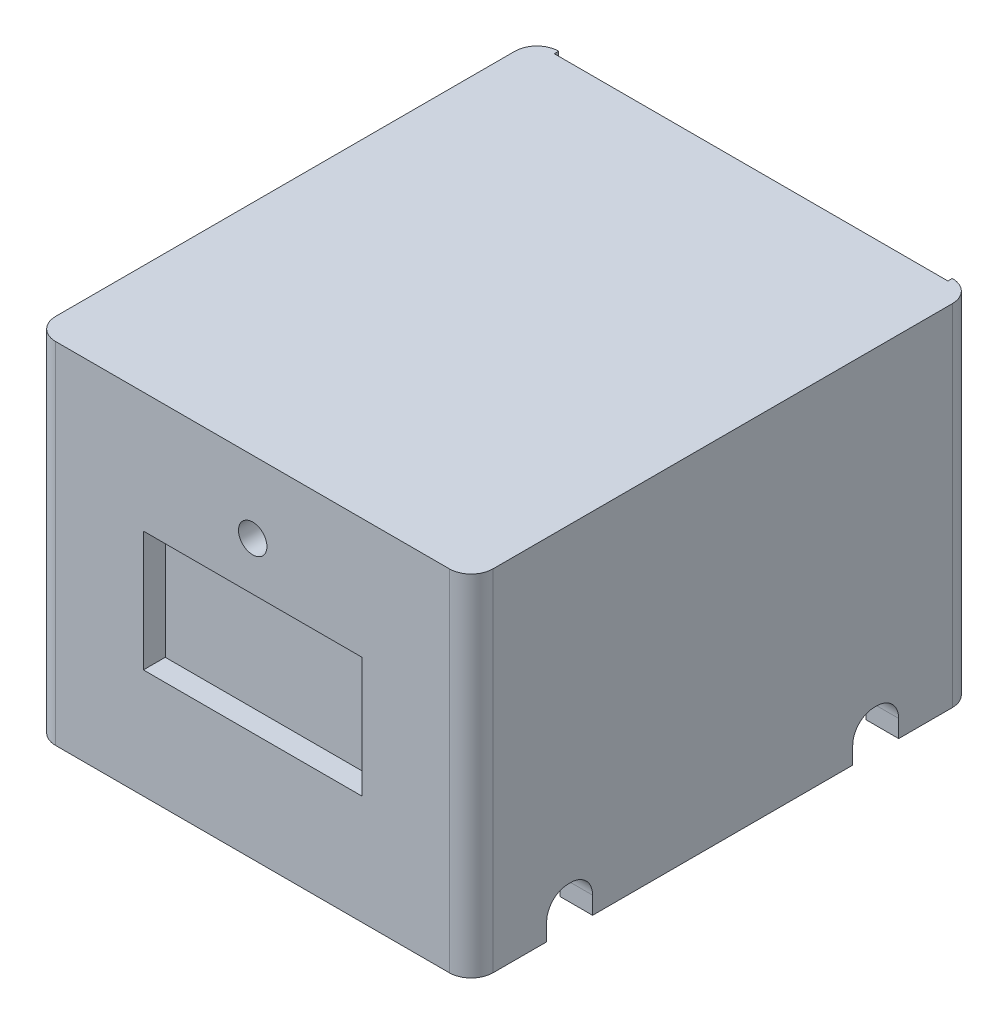
SolidWorks part; units mm, degrees
ref_plane "Plan de face" through (0, 0, 0) normal (0, 0, 1) x (1, 0, 0)
ref_plane "Plan de dessus" through (0, 0, 0) normal (0, 1, 0) x (1, 0, 0)
ref_plane "Plan de droite" through (0, 0, 0) normal (1, 0, 0) x (0, 0, -1)
sketch "Esquisse1" plane through (0, 0, 0) normal (0, 0, 1) x (1, 0, 0)
  line L1 (0, 0) -> (200, 0)
  line L2 (0, 0) -> (0, 160)
  line L3 (0, 160) -> (200, 160)
  line L4 (200, 0) -> (200, 160)
  dimension "D1" = 160
  dimension "D2" = 200
extrude "Boss.-Extru.1" add sketch "Esquisse1" along normal blind 230
fillet "Congé1" radius 10 4 edges at (0, 80, 230) (200, 80, 230) (200, 80, 0) (0, 80, 0)
sketch "Esquisse2" plane through (0, 0, 0) normal (0, -1, 0) x (1, 0, 0)
  line L0 (0, 220) -> (0, 10) construction
  line L1 (15, 215) -> (185, 215)
  line L2 (15, 215) -> (15, 15)
  line L3 (15, 15) -> (185, 15)
  line L4 (185, 215) -> (185, 15)
  line L5 (200, 220) -> (200, 10) construction
  line L6 (10, 230) -> (190, 230) construction
  line L7 (10, 0) -> (190, 0) construction
  dimension "D1" = 15
  dimension "D2" = 15
  dimension "D3" = 15
  dimension "D4" = 15
extrude "Enlèv. mat.-Extru.1" cut sketch "Esquisse2" against normal blind 20
sketch "Esquisse3" plane through (0, 0, 0) normal (0, -1, 0) x (-1, 0, 0)
  line L0 (-185, -15) -> (-185, -215) construction
  line L6 (-100, -230) -> (-100, 0) construction
  line L7 (-15, -34.5133) -> (-15, -55.5133)
  line L8 (0, -55.5133) -> (-15, -55.5133)
  line L9 (0, -34.5133) -> (0, -55.5133)
  line L10 (0, -34.5133) -> (-15, -34.5133)
  line L11 (-10, -230) -> (-190, -230) construction
  line L12 (-10, 0) -> (-190, 0) construction
  line L13 (-200, -34.5133) -> (-185, -34.5133)
  line L14 (-200, -34.5133) -> (-200, -55.5133)
  line L15 (-200, -55.5133) -> (-185, -55.5133)
  line L16 (-185, -34.5133) -> (-185, -55.5133)
  line L21 (-200, -115) -> (6.2528, -115) construction
  line L22 (-200, -220) -> (-200, -10) construction
  line L23 (-185, -195.4867) -> (-185, -174.4867)
  line L24 (-200, -174.4867) -> (-185, -174.4867)
  line L25 (-200, -195.4867) -> (-200, -174.4867)
  line L26 (-200, -195.4867) -> (-185, -195.4867)
  line L27 (0, -195.4867) -> (-15, -195.4867)
  line L28 (0, -195.4867) -> (0, -174.4867)
  line L29 (0, -174.4867) -> (-15, -174.4867)
  line L30 (-15, -195.4867) -> (-15, -174.4867)
  dimension "D1" = 21
extrude "Enlèv. mat.-Extru.2" cut sketch "Esquisse3" against normal blind 18
fillet "Congé2" radius 10 2 edges at (192.5, 18, 55.5133) (192.5, 18, 34.5133)
fillet "Congé3" radius 10 2 edges at (7.5, 18, 55.5133) (7.5, 18, 34.5133)
sketch "Esquisse5" plane through (0, 160, 0) normal (0, 1, 0) x (1, 0, 0)
sketch "Esquisse6" plane through (0, 0, 0) normal (0, 0, -1) x (-1, 0, 0)
  line L0 (-10, 0) -> (-10, 160) construction
  line L1 (-190, 158) -> (-10, 158)
  line L2 (-190, 158) -> (-190, 34)
  line L3 (-190, 34) -> (-10, 34)
  line L4 (-10, 158) -> (-10, 34)
  line L5 (-10, 0) -> (-190, 0) construction
  line L6 (-190, 160) -> (-190, 0) construction
  line L7 (-190, 160) -> (-10, 160) construction
  dimension "D1" = 2
  dimension "D2" = 34
extrude "Enlèv. mat.-Extru.4" cut sketch "Esquisse6" against normal blind 130
sketch "Esquisse7" plane through (0, 0, 0) normal (0, 0, -1) x (-1, 0, 0)
  line L1 (-190, 160) -> (-10, 160)
  line L2 (-190, 160) -> (-190, 158)
  line L3 (-190, 158) -> (-10, 158)
  line L4 (-10, 160) -> (-10, 158)
extrude "Enlèv. mat.-Extru.5" cut sketch "Esquisse7" against normal blind 2
fillet "Congé5" radius 10 4 edges at (7.5, 18, 174.4867) (7.5, 18, 195.4867) (192.5, 18, 195.4867) (192.5, 18, 174.4867)
sketch "Esquisse8" plane through (0, 0, 230) normal (0, 0, 1) x (1, 0, 0)
  circle A0 centre (100.0865, 127.0811) radius 6.5
  dimension "D1" = 13
extrude "Enlèv. mat.-Extru.6" cut sketch "Esquisse8" against normal blind 15
sketch "Esquisse9" plane through (0, 0, 230) normal (0, 0, 1) x (1, 0, 0)
  line L1 (50.0865, 105) -> (150.0865, 105)
  line L2 (50.0865, 105) -> (50.0865, 50)
  line L3 (50.0865, 50) -> (150.0865, 50)
  line L4 (150.0865, 105) -> (150.0865, 50)
  line L8 (10, 0) -> (190, 0) construction
  circle A1 centre (100.0865, 127.0811) radius 6.5 construction
  circle A2 centre (100.0865, 127.0811) radius 6.5 construction
  dimension "D1" = 50
  dimension "D2" = 50
  dimension "D3" = 55
  dimension "D4" = 50
extrude "Enlèv. mat.-Extru.7" cut sketch "Esquisse9" against normal blind 10
